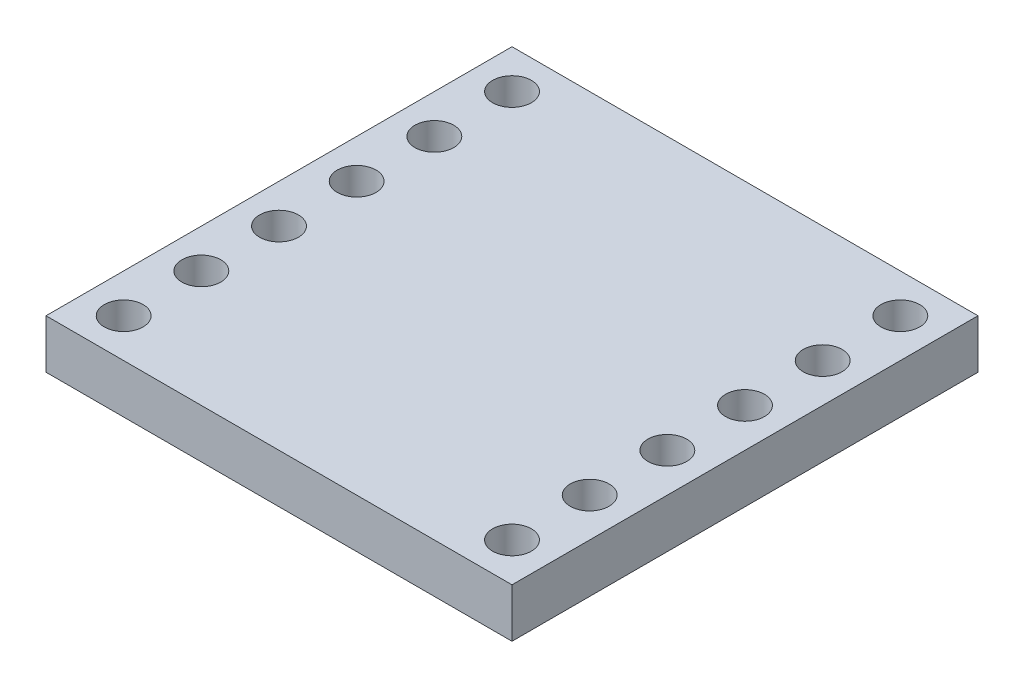
SolidWorks part; units mm, degrees
material "Plain Carbon Steel"
ref_plane "Front" through (0, 0, 0) normal (0, 0, 1) x (1, 0, 0)
ref_plane "Top" through (0, 0, 0) normal (0, 1, 0) x (1, 0, 0)
ref_plane "Right" through (0, 0, 0) normal (1, 0, 0) x (0, 0, -1)
sketch "Sketch1" plane through (0, 0, 0) normal (0, 1, 0) x (1, 0, 0)
  line L0 (0, 7.62) -> (0, -7.62)
  line L1 (0, 7.62) -> (-7.62, 7.62)
  line L3 (-7.62, -7.62) -> (0, -7.62)
  line L4 (-6.35, 6.35) -> (-6.35, 3.81) construction
  line L5 (-6.35, 3.81) -> (-6.35, 1.27) construction
  line L6 (-6.35, 1.27) -> (-6.35, -1.27) construction
  line L7 (-6.35, -1.27) -> (-6.35, -3.81) construction
  line L8 (-6.35, -3.81) -> (-6.35, -6.35) construction
  line L9 (-6.35, 0) -> (0, 0) construction
  line L10 (-7.62, 7.62) -> (-7.62, 0)
  line L11 (-7.62, 0) -> (-7.62, -7.62)
  circle A0 centre (-6.35, 6.35) radius 0.635
  circle A1 centre (-6.35, 3.81) radius 0.635
  circle A2 centre (-6.35, 1.27) radius 0.635
  circle A3 centre (-6.35, -1.27) radius 0.635
  circle A4 centre (-6.35, -3.81) radius 0.635
  circle A5 centre (-6.35, -6.35) radius 0.635
  point P0 (-6.35, 6.35)
  point P4 (0, 0)
  point P8 (-6.35, 3.81)
  point P9 (-6.35, 1.27)
  point P10 (-6.35, -1.27)
  point P11 (-6.35, -3.81)
  point P12 (-6.35, -6.35)
  dimension "D4" = 1.27
  dimension "D1" = 6.35
  dimension "D2" = 2.54
  dimension "D3" = 15.24
extrude "Boss-Extrude1" add sketch "Sketch1" along normal blind 1.6
mirror "Mirror1" about plane through (0, 1.6, -7.62) normal (-1, 0, 0) of "Boss-Extrude1"
